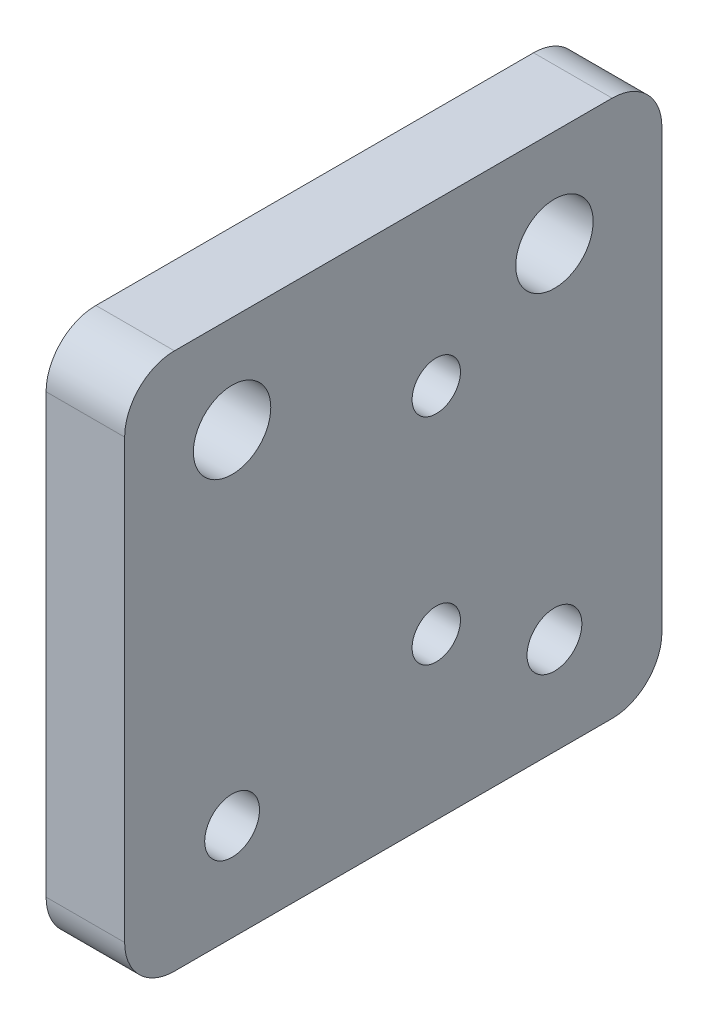
SolidWorks part; units mm, degrees
ref_plane "Front" through (0, 0, 0) normal (0, 0, 1) x (1, 0, 0)
ref_plane "Top" through (0, 0, 0) normal (0, 1, 0) x (1, 0, 0)
ref_plane "Right" through (0, 0, 0) normal (1, 0, 0) x (0, 0, -1)
sketch "Sketch2" plane through (0, 0, 0) normal (1, 0, 0) x (0, 0, -1)
  line L1 (-25, -25) -> (25, -25)
  line L2 (-25, -25) -> (-25, 25)
  line L3 (-25, 25) -> (25, 25)
  line L4 (25, -25) -> (25, 25)
  line L5 (0, 25) -> (0, -25) construction
  line L6 (-25, 0) -> (25, 0) construction
  point P0 (0, 0)
  dimension "D1" = 50
  dimension "D2" = 50
extrude "Boss-Extrude1" add sketch "Sketch2" along normal blind 7.31
sketch "Sketch6" plane through (0, 0, 0) normal (1, 0, 0) x (0, 0, -1)
  line L1 (15, -15.95) -> (-15, -15.95) construction
  line L2 (15, -15.95) -> (15, 15.95) construction
  line L3 (15, 15.95) -> (-15, 15.95) construction
  line L4 (-15, -15.95) -> (-15, 15.95) construction
  line L5 (0, 15.95) -> (0, -15.95) construction
  line L6 (15, 0) -> (-15, 0) construction
  circle A0 centre (-15, 15.95) radius 3.6
  circle A1 centre (15, 15.95) radius 3.6
  circle A2 centre (-15, -15.95) radius 2.55
  circle A3 centre (15, -15.95) radius 2.55
  point P0 (0, 0)
  dimension "D3" = 7.2
  dimension "D4" = 5.1
  dimension "D1" = 31.9
  dimension "D2" = 30
extrude "Cut-Extrude2" cut sketch "Sketch6" along normal through all
sketch "Sketch7" plane through (0, 0, 0) normal (-1, 0, 0) x (0, 0, 1)
  circle A0 centre (-15, -15.95) radius 5.05
  circle A1 centre (15, -15.95) radius 5.05
  circle A2 centre (-15, 15.95) radius 6
  circle A3 centre (15, 15.95) radius 6
  dimension "D1" = 12
  dimension "D2" = 10.1
extrude "Cut-Extrude3" cut sketch "Sketch7" against normal blind 2
hole_wizard "M4 Clearance Hole1" positions "Sketch11" profile "Sketch12" hole size "M4" standard "ANSI Metric" end condition through all
sketch "Sketch11" plane through (7.31, 0, 0) normal (1, 0, 0) x (0, 0, -1)
  line L2 (4, -10) -> (4, 10) construction
  line L5 (0, 0) -> (4, 0) construction
  point P0 (4, -10)
  point P2 (4, 10)
  point P16 (3.0063, -2.6385)
  point P17 (0.6648, -9.1864)
  dimension "D1" = 20
  dimension "D2" = 4
sketch "Sketch12" plane through (7.31, -10, -4) normal (0, 1, 0) x (0, 0, -1)
  line L0 (0, 0) -> (0, 7.31)
  line L1 (0, 7.31) -> (2.25, 7.31)
  line L2 (2.25, 7.31) -> (2.25, 0)
  line L5 (2.25, 0) -> (0, 0)
  line L11 (0, -6.35) -> (0, 107.95) construction
  dimension "Thru Hole Dia." = 4.5
  dimension "Thru Hole Depth" = 7.31
fillet "Fillet1" radius 4.635 4 edges at (3.655, -25, -25) (3.655, -25, 25) (3.655, 25, -25) (3.655, 25, 25)
